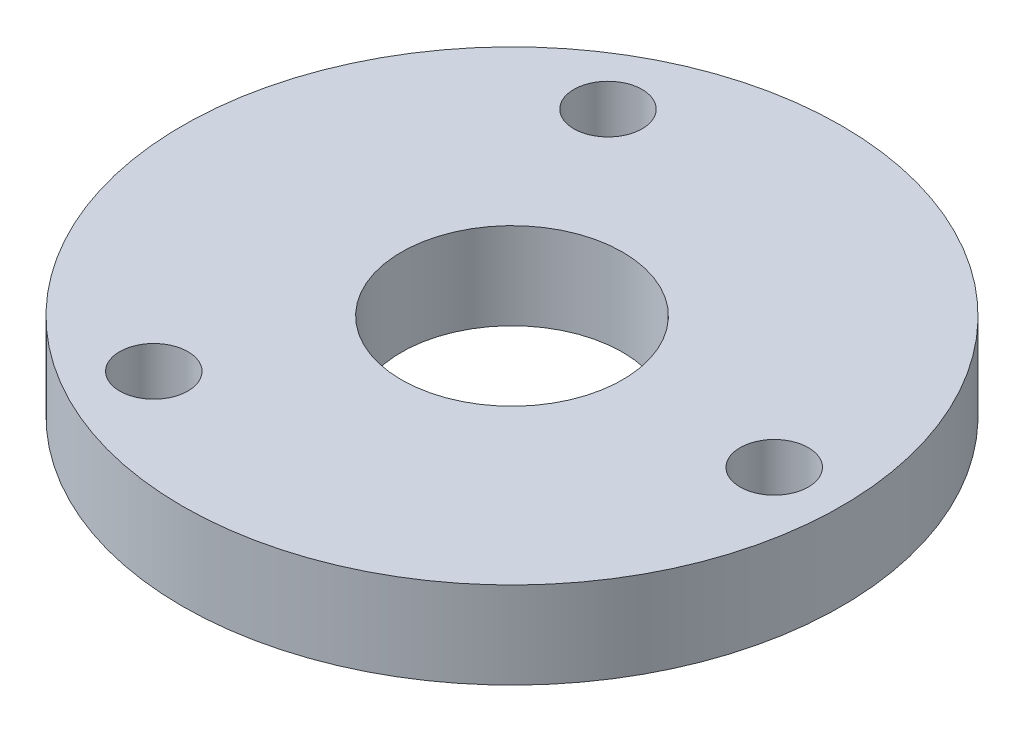
SolidWorks part; units mm, degrees
material "ABS"
ref_plane "Front Plane" through (0, 0, 0) normal (0, 0, 1) x (1, 0, 0)
ref_plane "Top Plane" through (0, 0, 0) normal (0, 1, 0) x (1, 0, 0)
ref_plane "Right Plane" through (0, 0, 0) normal (1, 0, 0) x (0, 0, -1)
sketch "Sketch1" plane through (0, 0, 0) normal (0, 1, 0) x (1, 0, 0)
  line L0 (13, 0) -> (25.4, 0) construction
  line L2 (19.2, 0) -> (9.6, 16.6277) construction
  line L3 (9.6, 16.6277) -> (-9.6, 16.6277) construction
  line L4 (-9.6, 16.6277) -> (-19.2, 0) construction
  line L5 (-19.2, 0) -> (-9.6, -16.6277) construction
  line L6 (-9.6, -16.6277) -> (9.6, -16.6277) construction
  line L7 (9.6, -16.6277) -> (19.2, 0) construction
  circle A0 centre (0, 0) radius 24.13
  circle A1 centre (0, 0) radius 25.4 construction
  circle A2 centre (0, 0) radius 13 construction
  circle A3 centre (19.2, 0) radius 2.5
  circle A4 centre (0, 0) radius 16.6277 construction
  circle A5 centre (-9.6, 16.6277) radius 2.5
  circle A6 centre (-9.6, -16.6277) radius 2.5
  circle A7 centre (0, 0) radius 8.1
  dimension "D1" = 48.26
  dimension "D2" = 50.8
  dimension "D3" = 26
  dimension "D4" = 5
  dimension "D5" = 5
  dimension "D6" = 5
  dimension "D7" = 16.2
extrude "Boss-Extrude1" add sketch "Sketch1" along normal blind 6.35
sketch "Sketch2" plane through (0, 6.35, 0) normal (0, 1, 0) x (1, 0, 0)
  line L1 (9.525, 0) -> (4.7625, 8.2489)
  line L2 (4.7625, 8.2489) -> (-4.7625, 8.2489)
  line L3 (-4.7625, 8.2489) -> (-9.525, 0)
  line L4 (-9.525, 0) -> (-4.7625, -8.2489)
  line L5 (-4.7625, -8.2489) -> (4.7625, -8.2489)
  line L6 (4.7625, -8.2489) -> (9.525, 0)
  circle A0 centre (0, 0) radius 8.2489 construction
  dimension "D1" = 9.525
sketch "Sketch3" plane through (0, 6.35, 0) normal (0, 1, 0) x (1, 0, 0)
  circle A0 centre (0, 0) radius 6.1
  circle A1 centre (0, 0) radius 8.2489 construction
  circle A2 centre (0, 0) radius 8.2489
  dimension "D1" = 12.2
